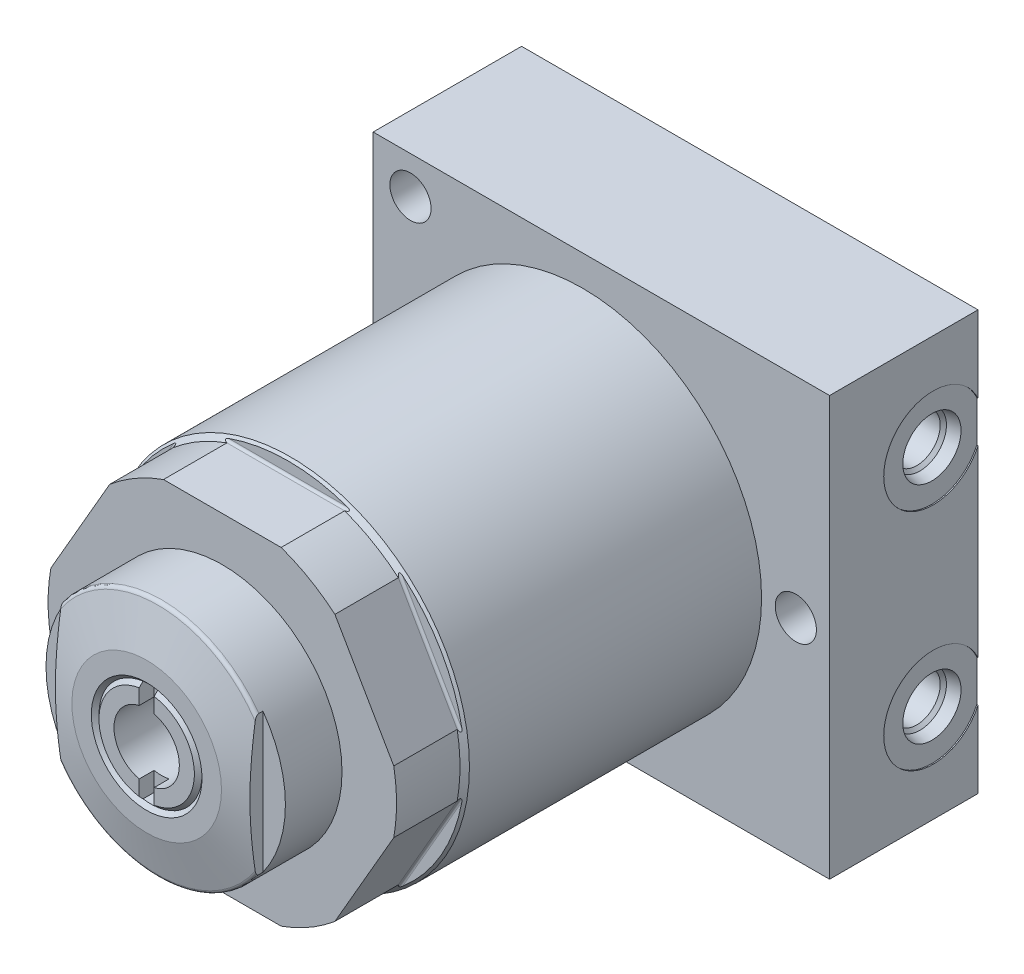
SolidWorks part; units mm, degrees
material "Alloy Steel"
ref_plane "Front Plane" through (0, 0, 0) normal (0, 0, 1) x (1, 0, 0)
ref_plane "Top Plane" through (0, 0, 0) normal (0, 1, 0) x (1, 0, 0)
ref_plane "Right Plane" through (0, 0, 0) normal (1, 0, 0) x (0, 0, -1)
ref_plane "Plane1" through (0, 0, 0) normal (0, 0, 1) x (1, 0, 0)
sketch "Sketch1" plane through (0, 0, 0) normal (0, 0, 1) x (1, 0, 0)
  circle A0 centre (0, 0) radius 37.973
  dimension "D1" = 75.946
extrude "Extrude1" add sketch "Sketch1" along normal blind 96.8502
ref_plane "Plane2" through (0, 0, 0) normal (1, 0, 0) x (0, 0, 1)
sketch "Sketch2" plane through (0, 0, 0) normal (1, 0, 0) x (0, 0, 1)
  line L0 (82.8802, 37.973) -> (82.8802, 35.306)
  line L1 (83.3882, 34.798) -> (96.8502, 34.798)
  line L2 (82.1817, 0) -> (97.5487, 0) construction
  line L3 (82.8802, 37.973) -> (96.8502, 37.973)
  line L4 (96.8502, -37.973) -> (96.8502, 37.973) construction
  line L5 (96.8502, 37.973) -> (0, 37.973) construction
  line L6 (96.8502, 37.973) -> (96.8502, 34.798)
  arc A0 (82.8802, 35.306) -> (83.3882, 34.798) centre (83.3882, 35.306) ccw
  dimension "D1" = 0.508
  dimension "D2" = 13.97
  dimension "D3" = 69.596
extrude "Cut-Extrude1" cut sketch "Sketch2" against normal mid plane 91.1352
ref_plane "Plane12" through (0, 0, 0) normal (1, 0, 0) x (0, 0, -1)
sketch "Sketch10" plane through (0, 0, 0) normal (1, 0, 0) x (0, 0, -1)
  line L0 (-96.8502, 36.9697) -> (-83.3882, 36.9697)
  line L1 (-83.3882, 36.9697) -> (-82.3849, 37.973)
  line L2 (-82.3849, 37.973) -> (-96.8502, 37.973)
  line L3 (-96.8502, 37.973) -> (-96.8502, 36.9697)
  line L4 (-97.5735, 0) -> (-81.6616, 0) construction
  line L5 (0, 37.973) -> (-96.8502, 37.973) construction
  line L6 (-96.8502, 37.973) -> (-96.8502, -34.798) construction
  dimension "D1" = 73.9394
  dimension "D2" = 13.462
  dimension "D3" = 45
revolve "Cut-Revolve1" cut sketch "Sketch10" angle 360 about L4
ref_plane "Plane15" through (0, 0, 0) normal (1, 0, 0) x (0, 0, -1)
sketch "Sketch13" plane through (0, 0, 0) normal (1, 0, 0) x (0, 0, -1)
  line L0 (-96.8502, 0) -> (-112.903, 0)
  line L1 (-112.903, 0) -> (-112.903, 25.4)
  line L2 (-112.903, 25.4) -> (-96.8502, 25.4)
  line L3 (-96.8502, 25.4) -> (-96.8502, 0)
  line L4 (-113.599, 0) -> (-66.4623, 0) construction
  line L5 (-96.8502, 36.9697) -> (-96.8502, -34.798) construction
  dimension "D1" = 50.8
  dimension "D2" = 16.0528
revolve "Revolve1" add sketch "Sketch13" angle 360 about L4
ref_plane "Plane16" through (-6.9342, 0, 112.8014) normal (0, 1, 0) x (-1, 0, 0)
sketch "S2D0011" plane through (-6.9342, 0, 112.8014) normal (0, 1, 0) x (-1, 0, 0)
  line L0 (0, 0.1016) -> (0, -15.9004)
  line L1 (0, -15.9004) -> (-6.9342, -15.9004)
  line L2 (0, 0.1016) -> (-6.9342, 0.1016)
  line L3 (-6.9342, 0.1016) -> (-6.9342, -15.9004)
  line L4 (-6.9342, -40.9554) -> (-6.9342, 0.8001) construction
  line L5 (18.4658, 0.1016) -> (-32.3342, 0.1016) construction
  dimension "D1" = 16.002
  dimension "D2" = 13.8684
revolve "Cut-Revolve4" cut sketch "S2D0011" angle 360 about L4
ref_plane "Plane17" through (0, 0, 0) normal (1, 0, 0) x (0, 0, -1)
sketch "Sketch15" plane through (0, 0, 0) normal (1, 0, 0) x (0, 0, -1)
  line L0 (-112.903, 15.875) -> (-110.5131, 24.7975)
  line L1 (-112.9602, 0) -> (-99.3181, 0) construction
  line L2 (-112.903, 25.4) -> (-112.903, -25.4) construction
  line L3 (-96.8502, 25.4) -> (-112.903, 25.4) construction
  line L4 (-109.728, 25.4) -> (-112.903, 25.4)
  line L5 (-112.903, 25.4) -> (-112.903, 15.875)
  arc A0 (-109.728, 25.4) -> (-110.5131, 24.7975) centre (-109.728, 24.5872) ccw
  dimension "D3" = 0.8128
  dimension "D1" = 31.75
  dimension "D2" = 3.175
revolve "Cut-Revolve5" cut sketch "Sketch15" angle 360 about L1
ref_plane "Plane18" through (0, 0, 0) normal (0, 1, 0) x (-1, 0, 0)
sketch "Sketch16" plane through (0, 0, 0) normal (0, 1, 0) x (-1, 0, 0)
  line L0 (-52.4002, -11.0998) -> (44.45, -11.0998)
  line L1 (44.45, -11.0998) -> (44.45, 20.3962)
  line L2 (44.45, 20.3962) -> (-52.4002, 20.3962)
  line L3 (-52.4002, 20.3962) -> (-52.4002, -11.0998)
  dimension "D1" = 11.0998
  dimension "D2" = 31.496
  dimension "D3" = 96.8502
  dimension "D4" = 44.45
extrude "Extrude2" add sketch "Sketch16" along normal blind 44.45 and the other way blind 44.45
sketch "Sketch17" plane through (52.4002, 0, 0) normal (1, 0, 0) x (0, 0, -1)
  line L0 (11.0998, -44.45) -> (11.0998, 44.45) construction
  circle A0 centre (1.5748, -23.8252) radius 10.4775
  dimension "D3" = 20.955
  dimension "D1" = 23.8252
  dimension "D2" = 9.525
extrude "Cut-Extrude9" cut sketch "Sketch17" against normal blind 0.254
sketch "Sketch18" plane through (52.4002, 0, 0) normal (1, 0, 0) x (0, 0, -1)
  line L0 (11.0998, -19.4603) -> (11.0998, 44.45) construction
  circle A0 centre (1.5748, 23.8252) radius 10.4775
  dimension "D2" = 20.955
  dimension "D1" = 23.8252
  dimension "D3" = 9.525
extrude "Cut-Extrude10" cut sketch "Sketch18" against normal blind 0.254
ref_plane "Plane19" through (52.1462, -23.8125, -1.5748) normal (0, 0, 1) x (0, -1, 0)
sketch "S2D0002" plane through (52.1462, -23.8125, -1.5748) normal (0, 0, 1) x (0, -1, 0)
  line L0 (0.0127, 0) -> (6.1976, 0)
  line L1 (6.1976, 0) -> (5.655, -2.5527)
  line L2 (5.655, -2.5527) -> (4.9911, -3.2166)
  line L3 (4.9911, -3.2166) -> (4.9911, -17.272)
  line L4 (4.9911, -17.272) -> (0.0127, -17.272)
  line L5 (0.0127, -17.272) -> (0.0127, 0)
  line L6 (0.0127, -20.698) -> (0.0127, 0.8636) construction
  dimension "D1" = 17.272
  dimension "D2" = 23.8252
revolve "Cut-Revolve6" cut sketch "S2D0002" angle 360 about L6
ref_plane "Plane20" through (52.1462, 23.8125, -1.5748) normal (0, 0, 1) x (0, -1, 0)
sketch "S2D0001" plane through (52.1462, 23.8125, -1.5748) normal (0, 0, 1) x (0, -1, 0)
  line L0 (-0.0127, 0) -> (6.1722, 0)
  line L1 (6.1722, 0) -> (5.6296, -2.5527)
  line L2 (5.6296, -2.5527) -> (4.9657, -3.2166)
  line L3 (4.9657, -3.2166) -> (4.9657, -17.272)
  line L4 (4.9657, -17.272) -> (-0.0127, -17.272)
  line L5 (-0.0127, -17.272) -> (-0.0127, 0)
  line L6 (-0.0127, -20.8229) -> (-0.0127, 0.8636) construction
  dimension "D1" = 17.272
  dimension "D2" = 23.8252
revolve "Cut-Revolve7" cut sketch "S2D0001" angle 360 about L6
hole_wizard "Hole1" positions "Sketch22" profile "Sketch21" legacy end condition up to next
sketch "Sketch22" plane through (0, 0, 20.3962) normal (0, 0, 1) x (1, 0, 0)
  line L0 (0, 0) -> (-58.5128, 0) construction
  point P0 (-36.5252, -36.5252)
  point P6 (45.2374, 0)
  point P9 (-36.5252, 36.5252)
  dimension "D1" = 45.2374
  dimension "D2" = 36.5252
  dimension "D3" = 36.5252
  dimension "D4" = 73.0504
sketch "Sketch21" plane through (-36.5252, -36.5252, 20.3962) normal (1, 0, 0) x (0, -1, 0)
  line L0 (0, 0) -> (0, 31.496)
  line L1 (0, 31.496) -> (4.3688, 31.496)
  line L2 (4.3688, 31.496) -> (4.3688, 0)
  line L3 (4.3688, 0) -> (0, 0)
  line L4 (0, 110) -> (0, -10) construction
  dimension "Diameter" = 8.7376
  dimension "Depth" = 31.496
pattern_circular "CirPattern2" count 6 over 360 about axis through (0, 0, 0) along (0, 0, 1) of "Cut-Extrude1"
sketch "Sketch23" plane through (0, 0, 112.903) normal (0, 0, 1) x (1, 0, 0)
  line L0 (0, 0) -> (0, 23.4695) construction
  line L1 (-20.6375, 14.8072) -> (-20.6375, -14.8072)
  line L2 (20.6375, 14.8072) -> (20.6375, -14.8072)
  arc A1 (-20.6375, 14.8072) -> (-20.6375, -14.8072) centre (0, 0) ccw
  arc A2 (20.6375, -14.8072) -> (20.6375, 14.8072) centre (0, 0) ccw
  circle A3 centre (0, 0) radius 25.4 construction
  dimension "D1" = 41.275
extrude "Cut-Extrude11" cut sketch "Sketch23" against normal blind 4.0386
sketch "Sketch24" plane through (0, 0, 0) normal (0, 1, 0) x (1, 0, 0)
  line L0 (-10.1219, -112.903) -> (-10.9347, -112.0902)
  line L1 (-10.9347, -112.0902) -> (-11.7475, -112.903)
  line L2 (-11.7475, -112.903) -> (-10.1219, -112.903)
  line L3 (0, 10.0813) -> (0, 21.2783) construction
  line L5 (-15.875, -112.903) -> (15.875, -112.903) construction
  dimension "D1" = 45
  dimension "D2" = 1.6256
  dimension "D3" = 21.8694
revolve "Cut-Revolve8" cut sketch "Sketch24" angle 360 about L3
sketch "Sketch25" plane through (0, 0, 112.903) normal (0, 0, 1) x (1, 0, 0)
  line L0 (-1.5875, 10.8188) -> (-1.5875, -10.8188)
  line L1 (1.5875, -10.8188) -> (1.5875, 10.8188)
  line L2 (0, 13.5691) -> (0, 34.3644) construction
  arc A0 (-1.5875, -10.8188) -> (1.5875, -10.8188) centre (0, 0) ccw
  arc A1 (1.5875, 10.8188) -> (-1.5875, 10.8188) centre (0, 0) ccw
  circle A2 centre (0, 0) radius 10.9347 construction
  dimension "D2" = 3.175
extrude "Cut-Extrude12" cut sketch "Sketch25" against normal blind 3.175
